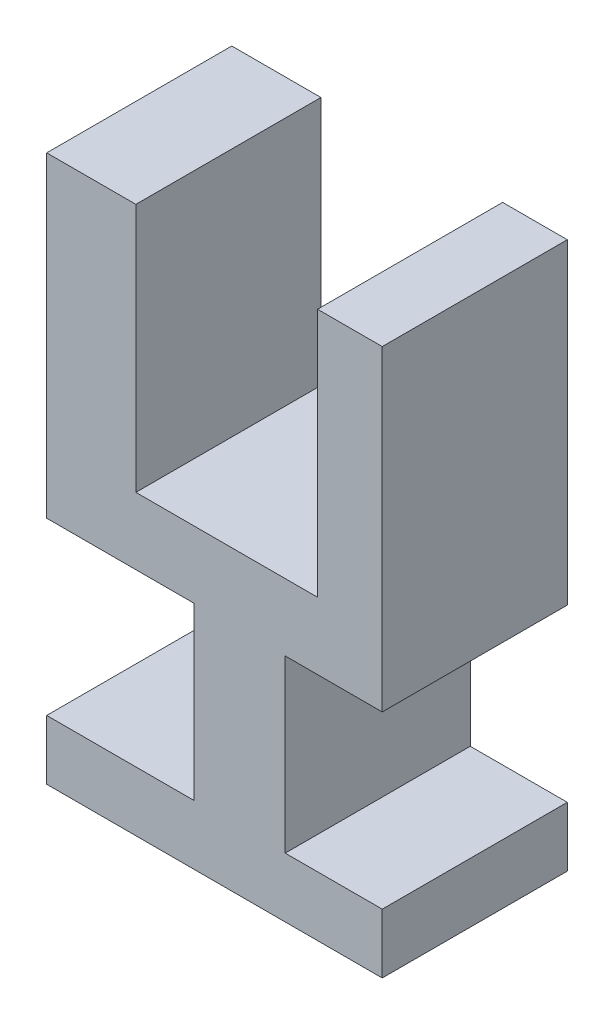
SolidWorks part; units mm, degrees
ref_plane "Front Plane" through (0, 0, 0) normal (0, 0, 1) x (1, 0, 0)
ref_plane "Top Plane" through (0, 0, 0) normal (0, 1, 0) x (1, 0, 0)
ref_plane "Right Plane" through (0, 0, 0) normal (1, 0, 0) x (0, 0, -1)
sketch "Sketch1" plane through (0, 0, 0) normal (0, 0, 1) x (1, 0, 0)
  line L0 (-51.9849, 41.4598) -> (-51.9849, -17.8469)
  line L1 (-51.9849, -17.8469) -> (-8.7862, -17.8469)
  line L2 (-8.7862, -17.8469) -> (-8.7862, 41.4598)
  line L3 (-8.7862, 41.4598) -> (6.5896, 41.4598)
  line L4 (6.5896, 41.4598) -> (6.5896, -33.7719)
  line L5 (6.5896, -33.7719) -> (-16.4782, -33.7719)
  line L6 (-16.4782, -33.7719) -> (-16.4782, -74.3741)
  line L7 (-16.4782, -74.3741) -> (6.5896, -74.3741)
  line L8 (6.5896, -74.3741) -> (6.5896, -88.5508)
  line L9 (6.5896, -88.5508) -> (-73.1849, -88.5508)
  line L10 (-73.1849, -88.5508) -> (-73.1849, -74.3741)
  line L11 (-73.1849, -74.3741) -> (-38.2158, -74.3741)
  line L12 (-38.2158, -74.3741) -> (-38.2158, -33.7719)
  line L13 (-38.2158, -33.7719) -> (-73.1849, -33.7719)
  line L14 (-73.1849, -33.7719) -> (-73.1849, 41.4598)
  line L15 (-73.1849, 41.4598) -> (-51.9849, 41.4598)
extrude "Boss-Extrude1" add sketch "Sketch1" along normal blind 44
